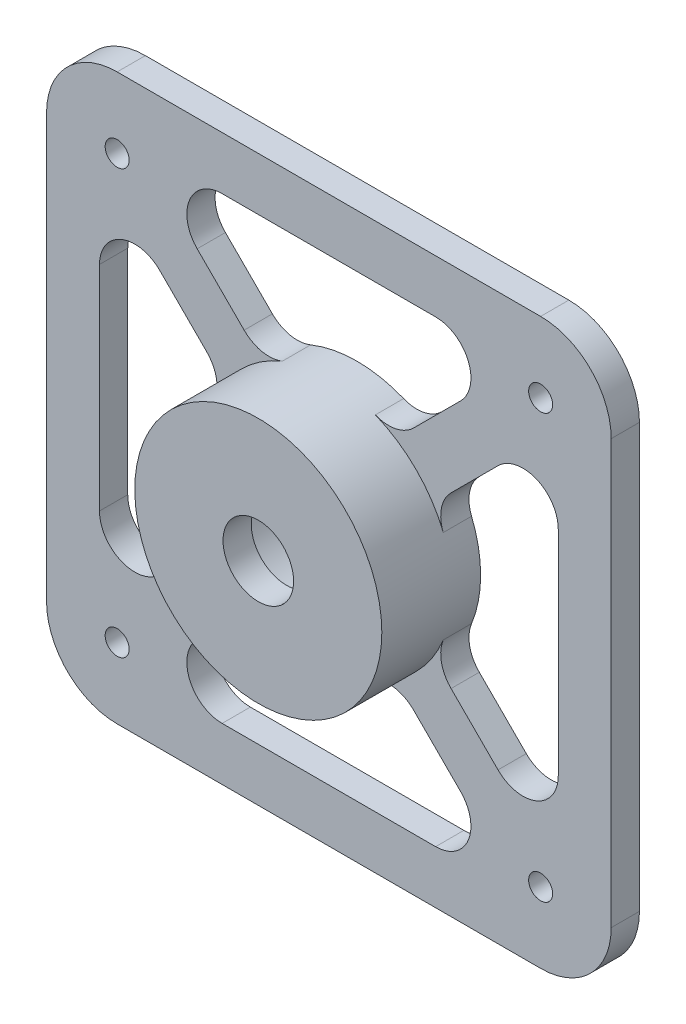
SolidWorks part; units mm, degrees
material "6061 Сплав"
ref_plane "Front" through (0, 0, 0) normal (0, 0, 1) x (1, 0, 0)
ref_plane "Top" through (0, 0, 0) normal (0, 1, 0) x (1, 0, 0)
ref_plane "Right" through (0, 0, 0) normal (1, 0, 0) x (0, 0, -1)
sketch "Sketch1" plane through (0, 0, 0) normal (0, 0, 1) x (1, 0, 0)
  line L1 (-40, -40) -> (40, -40)
  line L2 (-40, -40) -> (-40, 40)
  line L3 (-40, 40) -> (40, 40)
  line L4 (40, -40) -> (40, 40)
  line L5 (-40, -40) -> (40, 40) construction
  line L6 (-40, 40) -> (40, -40) construction
  point P0 (0, 0)
extrude "Boss-Extrude1" add sketch "Sketch1" along normal blind 4
sketch "Sketch2" plane through (0, 0, 0) normal (0, 0, 1) x (1, 0, 0)
  circle A0 centre (0, 0) radius 10
sketch "Sketch7" plane through (0, 0, 0) normal (0, 0, -1) x (-1, 0, 0)
  line L0 (17.3092, -12.0059) -> (23.9645, -18.6612)
  line L1 (-15.1256, -32.5) -> (15.1256, -32.5)
  line L2 (-32.5, -15.1256) -> (-32.5, 15.1256)
  line L3 (-15.1256, 32.5) -> (15.1256, 32.5)
  line L4 (32.5, -15.1256) -> (32.5, 15.1256)
  line L5 (-32.5, -32.5) -> (32.5, 32.5) construction
  line L6 (-32.5, 32.5) -> (32.5, -32.5) construction
  line L7 (12.0059, -17.3092) -> (18.6612, -23.9645)
  line L8 (-12.0059, -17.3092) -> (-18.6612, -23.9645)
  line L9 (-17.3092, -12.0059) -> (-23.9645, -18.6612)
  line L10 (-17.3092, 12.0059) -> (-23.9645, 18.6612)
  line L11 (-12.0059, 17.3092) -> (-18.6612, 23.9645)
  line L12 (12.0059, 17.3092) -> (18.6612, 23.9645)
  line L13 (17.3092, 12.0059) -> (23.9645, 18.6612)
  line L14 (-12.1006, 17.4039) -> (-17.4039, 12.1006) construction
  line L15 (17.7471, 12.4438) -> (12.4438, 17.7471) construction
  line L16 (17.6426, -12.3393) -> (12.3393, -17.6426) construction
  line L17 (-13.8538, -19.1571) -> (-19.1571, -13.8538) construction
  line L19 (-40, 40) -> (40, 40) construction
  arc A0 (6.5881, 16.2126) -> (-6.5881, 16.2126) centre (0, 0) ccw
  arc A2 (16.2126, -6.5881) -> (16.2126, 6.5881) centre (0, 0) ccw
  arc A3 (-6.5881, -16.2126) -> (6.5881, -16.2126) centre (0, 0) ccw
  arc A4 (-16.2126, 6.5881) -> (-16.2126, -6.5881) centre (0, 0) ccw
  arc A5 (-23.9645, 18.6612) -> (-32.5, 15.1256) centre (-27.5, 15.1256) ccw
  arc A6 (-17.3092, 12.0059) -> (-16.2126, 6.5881) centre (-20.8447, 8.4704) cw
  arc A7 (-17.3092, -12.0059) -> (-16.2126, -6.5881) centre (-20.8447, -8.4704) ccw
  arc A8 (-23.9645, -18.6612) -> (-32.5, -15.1256) centre (-27.5, -15.1256) cw
  arc A9 (-18.6612, -23.9645) -> (-15.1256, -32.5) centre (-15.1256, -27.5) ccw
  arc A10 (-12.0059, -17.3092) -> (-6.5881, -16.2126) centre (-8.4704, -20.8447) cw
  arc A11 (12.0059, -17.3092) -> (6.5881, -16.2126) centre (8.4704, -20.8447) ccw
  arc A12 (18.6612, -23.9645) -> (15.1256, -32.5) centre (15.1256, -27.5) cw
  arc A13 (23.9645, -18.6612) -> (32.5, -15.1256) centre (27.5, -15.1256) ccw
  arc A14 (17.3092, -12.0059) -> (16.2126, -6.5881) centre (20.8447, -8.4704) cw
  arc A15 (17.3092, 12.0059) -> (16.2126, 6.5881) centre (20.8447, 8.4704) ccw
  arc A16 (23.9645, 18.6612) -> (32.5, 15.1256) centre (27.5, 15.1256) cw
  arc A17 (18.6612, 23.9645) -> (15.1256, 32.5) centre (15.1256, 27.5) ccw
  arc A18 (12.0059, 17.3092) -> (6.5881, 16.2126) centre (8.4704, 20.8447) cw
  arc A19 (-6.5881, 16.2126) -> (-12.0059, 17.3092) centre (-8.4704, 20.8447) cw
  arc A20 (-18.6612, 23.9645) -> (-15.1256, 32.5) centre (-15.1256, 27.5) cw
  circle A22 centre (0, 0) radius 10 construction
  point P31 (-14.7522, 14.7522)
  point P32 (15.0955, 15.0955)
  point P33 (14.9909, -14.9909)
  point P34 (-16.5055, -16.5055)
  point P42 (-14.7386, 9.4353)
  point P51 (-9.4353, -14.7386)
  point P60 (14.7386, -9.4353)
  dimension "D1" = 7.5
  dimension "D2" = 7.5
  dimension "D4" = 5
  dimension "D3" = 7.5
extrude "Cut-Extrude3" cut sketch "Sketch7" against normal through all
sketch "Sketch8" plane through (0, 0, 4) normal (0, 0, 1) x (1, 0, 0)
  circle A0 centre (0, 0) radius 17.5
  arc A2 (16.2126, -6.5881) -> (16.2126, 6.5881) centre (0, 0) ccw construction
  point P4 (17.5, 0)
extrude "Boss-Extrude2" add sketch "Sketch8" along normal blind 10
sketch "Sketch3" plane through (0, 0, 4) normal (0, 0, 1) x (1, 0, 0)
  line L1 (-30, -30) -> (30, -30) construction
  line L2 (-30, -30) -> (-30, 30) construction
  line L3 (-30, 30) -> (30, 30) construction
  line L4 (30, -30) -> (30, 30) construction
  line L5 (-30, -30) -> (30, 30) construction
  line L6 (-30, 30) -> (30, -30) construction
  point P0 (0, 0)
  point P7 (-30, 30)
  point P8 (30, 30)
  point P9 (30, -30)
  point P10 (-30, -30)
hole_wizard "M3 Clearance Hole1" positions "Sketch5" profile "Sketch6" hole size "M3" standard "ANSI Metric" end condition through all
sketch "Sketch5" plane through (0, 0, 4) normal (0, 0, 1) x (1, 0, 0)
  point P0 (-30, 30)
  point P3 (30, 30)
  point P6 (30, -30)
  point P9 (-30, -30)
sketch "Sketch6" plane through (-30, 30, 4) normal (1, 0, 0) x (0, -1, 0)
  line L0 (0, 0) -> (0, 4)
  line L1 (0, 4) -> (1.7, 4)
  line L2 (1.7, 4) -> (1.7, 0)
  line L5 (1.7, 0) -> (0, 0)
  line L11 (0, -6.35) -> (0, 107.95) construction
  dimension "Thru Hole Dia." = 3.4
  dimension "Thru Hole Depth" = 4
fillet "Fillet1" radius 10 4 edges at (-40, 40, 2) (40, -40, 2) (-40, -40, 2) (40, 40, 2)
extrude "Cut-Extrude4" cut sketch "Sketch2" along normal blind 10 contours A0
sketch "Sketch9" plane through (0, 0, 14) normal (0, 0, 1) x (1, 0, 0)
  circle A0 centre (0, 0) radius 5
extrude "Cut-Extrude5" cut sketch "Sketch9" against normal through all
chamfer "Chamfer5" [suppressed] distance 0.5 angle 45
